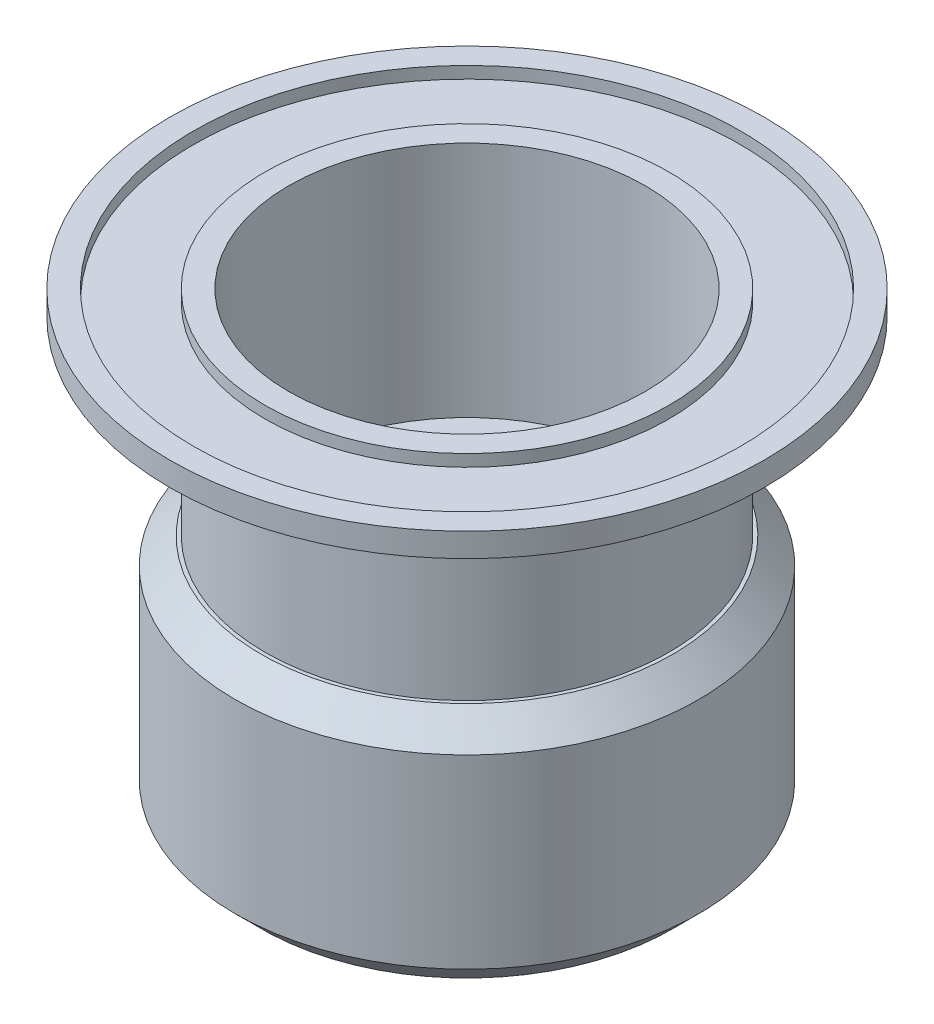
SolidWorks part; units mm, degrees
material "Сталь"
ref_plane "Спереди" through (0, 0, 0) normal (0, 0, 1) x (1, 0, 0)
ref_plane "Сверху" through (0, 0, 0) normal (0, 1, 0) x (1, 0, 0)
ref_plane "Справа" through (0, 0, 0) normal (1, 0, 0) x (0, 0, -1)
sketch "Эскиз2" plane through (0, 0, 0) normal (0, 0, 1) x (1, 0, 0)
  line L0 (15, 0) -> (15, -20)
  line L1 (0, 0) -> (0, -25.0757) construction
  line L2 (15, 0) -> (25, 0)
  line L3 (15, -20) -> (0, -20)
  line L4 (17, -22) -> (0, -22)
  line L5 (17, -2) -> (17, -22)
  line L6 (17, -2) -> (25, -2)
  line L7 (25, 0) -> (25, -2)
  line L8 (0, -20) -> (0, -22)
  dimension "D1" = 30
  dimension "D2" = 50
  dimension "D3" = 20
  dimension "D4" = 2
revolve "Повернуть1" add sketch "Эскиз2" angle 360 about L1
sketch "Эскиз3" plane through (0, 0, 0) normal (0, 1, 0) x (1, 0, 0)
  circle A2 centre (0, 0) radius 17
  circle A3 centre (0, 0) radius 17
  circle A5 centre (0, 0) radius 23
  circle A6 centre (0, 0) radius 23
  dimension "D1" = 2
  dimension "D2" = 2
extrude "Вырез-Вытянуть1" cut sketch "Эскиз3" against normal blind 1
sketch "Эскиз4" plane through (0, -20, 0) normal (0, 1, 0) x (1, 0, 0)
  line L1 (-5, -5) -> (5, -5)
  line L2 (-5, -5) -> (-5, 5)
  line L3 (-5, 5) -> (5, 5)
  line L4 (5, -5) -> (5, 5)
  line L5 (-5, -5) -> (5, 5) construction
  line L6 (-5, 5) -> (5, -5) construction
  point P0 (0, 0)
  dimension "D1" = 10
extrude "Вырез-Вытянуть2" cut sketch "Эскиз4" against normal blind 1.5
sketch "Эскиз5" plane through (0, -20, 0) normal (0, 1, 0) x (1, 0, 0)
  circle A0 centre (0, 0) radius 10 construction
  circle A1 centre (0, 10) radius 4
  circle A2 centre (10, 0) radius 4
  circle A3 centre (0, -10) radius 4
  circle A4 centre (-10, 0) radius 4
  point P14 (0, 0)
  dimension "D1" = 8
  dimension "D2" = 20
  dimension "D3" = 4
extrude "Вырез-Вытянуть3" cut sketch "Эскиз5" against normal through all
sketch "Эскиз9" plane through (0, -22, 0) normal (0, -1, 0) x (1, 0, 0)
  circle A0 centre (0, 10) radius 4 construction
  circle A1 centre (0, 0) radius 17
  circle A2 centre (0, 0) radius 17
  circle A3 centre (-10, 0) radius 4 construction
  circle A4 centre (0, -10) radius 4 construction
  circle A5 centre (10, 0) radius 4 construction
  circle A6 centre (0, 10) radius 4
  circle A7 centre (-10, 0) radius 4
  circle A8 centre (0, -10) radius 4
  circle A9 centre (10, 0) radius 4
  dimension "D1" = 0
extrude "Бобышка-Вытянуть1" add sketch "Эскиз9" along normal blind 1
sketch "Эскиз10" plane through (0, -23, 0) normal (0, -1, 0) x (1, 0, 0)
  circle A0 centre (0, 0) radius 15
  circle A1 centre (0, 0) radius 17
  circle A2 centre (0, 0) radius 17
  dimension "D1" = 0
  dimension "D2" = 2
extrude "Бобышка-Вытянуть2" add sketch "Эскиз10" along normal blind 15
sketch "Эскиз11" plane through (0, -21.5, 0) normal (0, 1, 0) x (1, 0, 0)
  circle A0 centre (0, 0) radius 2.75
  dimension "D1" = 5.5
extrude "Вырез-Вытянуть4" cut sketch "Эскиз11" against normal through all
sketch "Эскиз12" plane through (0, -38, 0) normal (0, -1, 0) x (1, 0, 0)
  circle A0 centre (0, 0) radius 19.5
  circle A1 centre (0, 0) radius 17 construction
  circle A2 centre (0, 0) radius 17
  dimension "D1" = 39
extrude "Бобышка-Вытянуть3" add sketch "Эскиз12" against normal blind 20
cosmetic thread "Условное изображение резьбы1" parameters "D2"=34.61
chamfer "Фаска1" distance 2.195 angle 45 2 edges at (0, -18, -19.5) (0, -38, -19.5)
